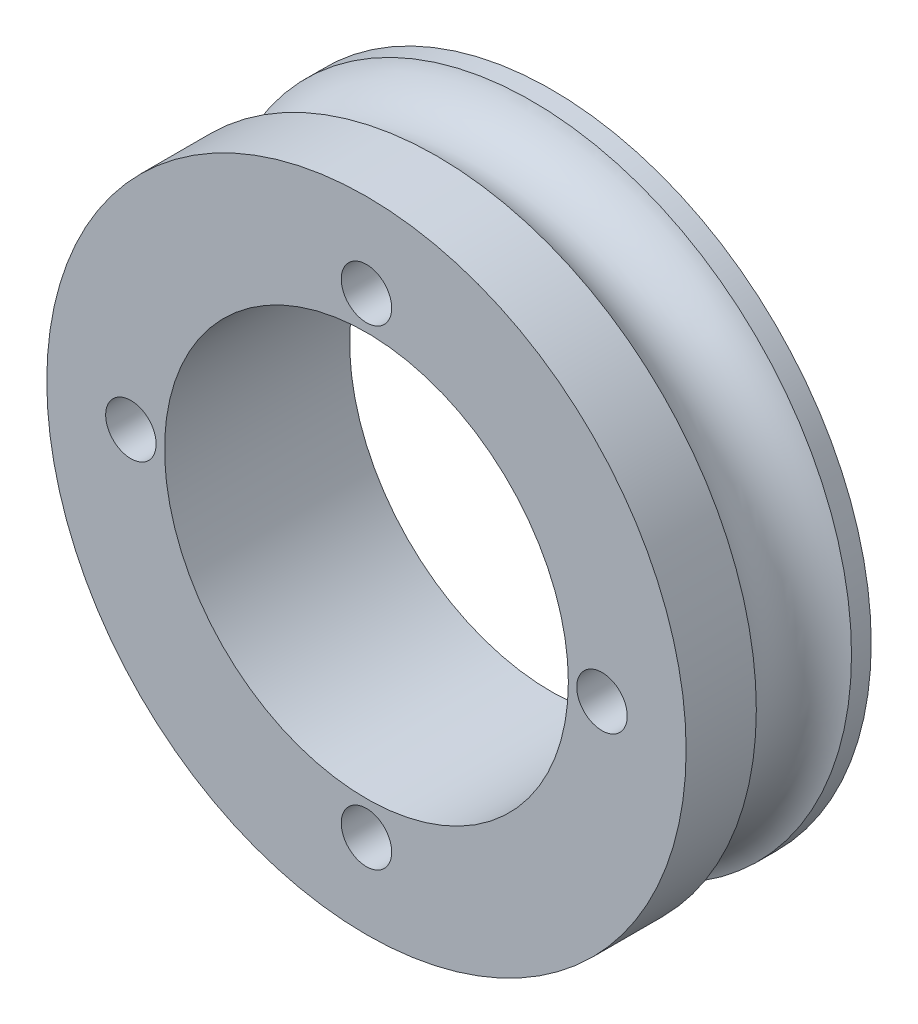
SolidWorks part; units mm, degrees
ref_plane "Piano frontale" through (0, 0, 0) normal (0, 0, 1) x (1, 0, 0)
ref_plane "Piano superiore" through (0, 0, 0) normal (0, 1, 0) x (1, 0, 0)
ref_plane "Piano destro" through (0, 0, 0) normal (1, 0, 0) x (0, 0, -1)
sketch "Schizzo1" plane through (0, 0, 0) normal (0, 0, 1) x (1, 0, 0)
  circle A0 centre (0, 0) radius 12
  circle A1 centre (0, 0) radius 19
  circle A2 centre (0, 0) radius 14 construction
  circle A3 centre (0, 14) radius 1.5
  circle A4 centre (14, 0) radius 1.5
  circle A5 centre (0, -14) radius 1.5
  circle A6 centre (-14, 0) radius 1.5
  dimension "D1" = 24
  dimension "D2" = 38
  dimension "D3" = 28
  dimension "D4" = 3
  dimension "D5" = 3
  dimension "D6" = 3
  dimension "D7" = 3
extrude "Estrusione-Estrusione1" add sketch "Schizzo1" along normal blind 11
ref_axis "Assi1" through (0, 0, 11) along (0, 0, -1)
sketch "Schizzo2" plane through (0, 0, 0) normal (1, 0, 0) x (0, 0, -1)
  circle A0 centre (-4, 20) radius 3
  dimension "D1" = 6
  dimension "D2" = 20
  dimension "D3" = 4
revolve "Taglia-Rivoluzione1" cut sketch "Schizzo2" angle 360 about axis through (0, 0, 11) along (0, 0, -1)
